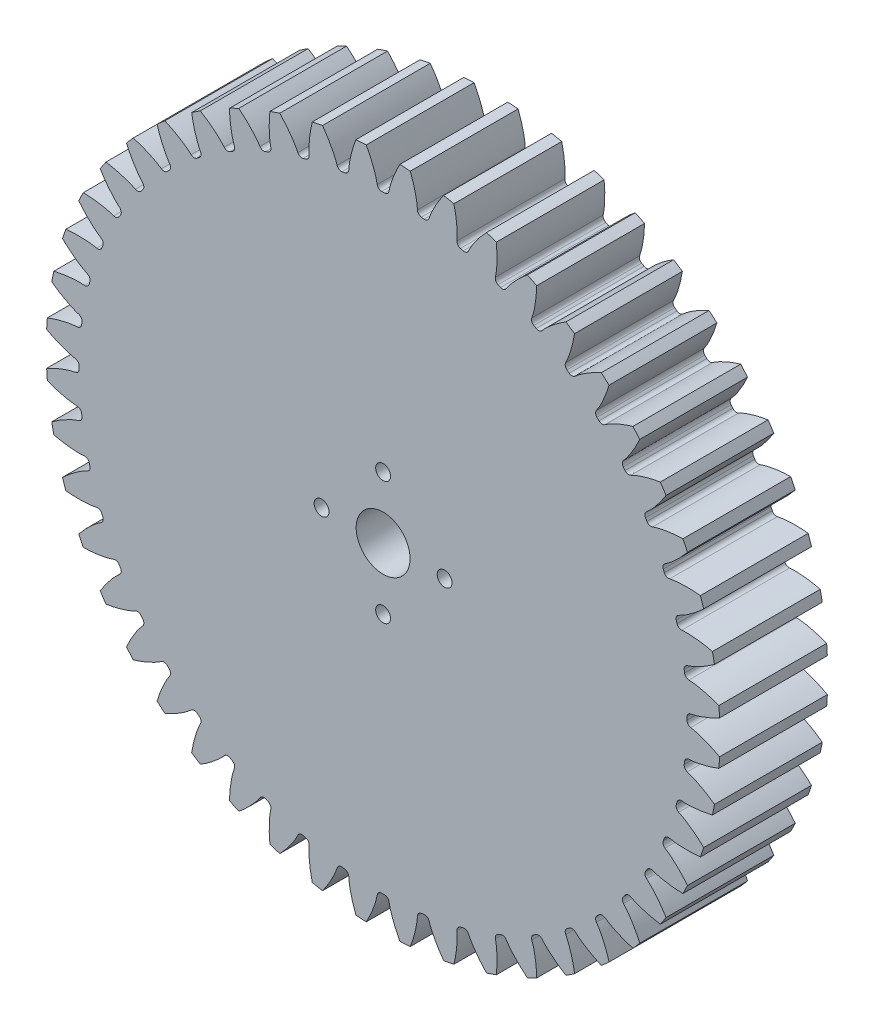
SolidWorks part; units mm, degrees
ref_plane "Front Plane" through (0, 0, 0) normal (0, 0, 1) x (1, 0, 0)
ref_plane "Top Plane" through (0, 0, 0) normal (0, 1, 0) x (1, 0, 0)
ref_plane "Right Plane" through (0, 0, 0) normal (1, 0, 0) x (0, 0, -1)
sketch "Sketch1" plane through (0, 0, 0) normal (0, 0, 1) x (1, 0, 0)
  line L0 (0, 0) -> (0, 38.1) construction
  line L1 (-12.2451, 42.5569) -> (12.2451, 33.6431) construction
  circle A0 centre (0, 0) radius 36.1156 construction
  circle A1 centre (0, 0) radius 39.6875 construction
  circle A2 centre (0, 0) radius 38.1 construction
  circle A3 centre (0, 0) radius 35.8023 construction
  circle A4 centre (0, 0) radius 3.175 construction
  circle A5 centre (0, 0) radius 6.35 construction
  point P8 (203.2, 0)
  point P13 (609.6, 0)
  dimension "OD | Outside Diameter" = 79.375
  dimension "Root Diameter" = 72.2313
  dimension "Gear Pitch Diameter" = 76.2
  dimension "Base Diameter" = 71.6046
  dimension "For Shaft Diameter" = 6.35
  dimension "Hub Diameter" = 12.7
  dimension "Pressure Angle" = 20
  dimension "Number of Teeth" = 1219.2
  dimension "Gear Pitch | Diametral Pitch" = 406.4
sketch "Sketch2" plane through (0, 0, 0) normal (1, 0, 0) x (0, 0, -1)
  line L0 (-6.35, 0) -> (6.35, 0) construction
  line L1 (-6.35, 39.6875) -> (6.35, 39.6875) construction
  point P2 (0, 39.6875)
  point P4 (-5.715, 0)
  point P6 (-5.715, 39.6875)
  dimension "Overall Width" = 12.7
  dimension "Face Width" = 12.065
sketch "Sketch3" plane through (0, 0, 0) normal (0, 0, 1) x (1, 0, 0)
  circle A0 centre (0, 0) radius 39.6875
  circle A1 centre (0, 0) radius 39.6875 construction
extrude "Boss-Extrude1" add sketch "Sketch3" against normal up to vertex (6.35 mm away) and the other way up to vertex (6.35 mm away) up to point (0, 0, -6.35) other way up to point (0, 0, 6.35)
sketch "Sketch4" plane through (0, 0, 0) normal (0, 0, 1) x (1, 0, 0)
  line L0 (0, 0) -> (35.7965, 0.638) construction
  line L2 (0, 0) -> (35.7965, -0.638) construction
  line L4 (35.7965, 0.638) -> (35.7966, 0.638)
  line L5 (35.7966, -0.638) -> (35.7965, -0.638)
  arc A0 (35.7965, 0.638) -> (35.7965, -0.638) centre (0, 0) cw
  arc A3 (39.6379, 1.9832) -> (39.6379, -1.9832) centre (0, 0) cw
  circle A4 centre (0, 0) radius 39.6875 construction
  spline S0 degree 4 poles (35.7966, 0.638) (35.8027, 0.6382) (35.8196, 0.6388) (35.8517, 0.6408) (35.904, 0.6452) (35.9707, 0.6523) (36.0567, 0.6632) (36.1581, 0.6785) (36.2693, 0.6976) (36.3903, 0.7211) (36.5108, 0.7468) (36.631, 0.7746) (36.7506, 0.8043) (36.8954, 0.8425) (37.0688, 0.8916) (37.2712, 0.9536) (37.5005, 1.0294) (37.7337, 1.1125) (37.9629, 1.1992) (38.1941, 1.2923) (38.4174, 1.3864) (38.649, 1.4898) (38.8625, 1.5882) (39.1012, 1.7047) (39.2937, 1.8006) (39.5471, 1.9338) (39.6965, 2.0146) (39.8712, 2.1113) (39.9487, 2.1555) (39.9964, 2.1827) knots 0 0 0 0 0 0.005377 0.015084 0.028532 0.04661 0.064855 0.092111 0.119476 0.146842 0.174209 0.201575 0.228941 0.256307 0.307035 0.361767 0.4165 0.471232 0.525964 0.580697 0.635429 0.690161 0.744894 0.799626 0.854358 0.909091 0.954545 1 1 1 1 1 construction
  spline S1 degree 4 poles (35.7966, 0.638) (35.8027, 0.6382) (35.8196, 0.6388) (35.8517, 0.6408) (35.904, 0.6452) (35.9707, 0.6523) (36.0567, 0.6632) (36.1581, 0.6785) (36.2693, 0.6976) (36.3903, 0.7211) (36.5108, 0.7468) (36.631, 0.7746) (36.7506, 0.8043) (36.8954, 0.8425) (37.0688, 0.8916) (37.2712, 0.9536) (37.5005, 1.0294) (37.7337, 1.1125) (37.9629, 1.1992) (38.1941, 1.2923) (38.4174, 1.3864) (38.649, 1.4898) (38.8625, 1.5882) (39.1012, 1.7047) (39.2937, 1.8006) (39.4921, 1.905) (39.5886, 1.9565) (39.6379, 1.9832) knots 0 0 0 0 0 0.005377 0.015084 0.028532 0.04661 0.064855 0.092111 0.119476 0.146842 0.174209 0.201575 0.228941 0.256307 0.307035 0.361767 0.4165 0.471232 0.525964 0.580697 0.635429 0.690161 0.744894 0.799626 0.854358 0.909091 0.909091 0.909091 0.909091 0.909091
  spline S2 degree 4 poles (35.7966, -0.638) (35.8027, -0.6382) (35.8196, -0.6388) (35.8517, -0.6408) (35.904, -0.6452) (35.9707, -0.6523) (36.0567, -0.6632) (36.1581, -0.6785) (36.2693, -0.6976) (36.3903, -0.7211) (36.5108, -0.7468) (36.631, -0.7746) (36.7506, -0.8043) (36.8954, -0.8425) (37.0688, -0.8916) (37.2712, -0.9536) (37.5005, -1.0294) (37.7337, -1.1125) (37.9629, -1.1992) (38.1941, -1.2923) (38.4174, -1.3864) (38.649, -1.4898) (38.8625, -1.5882) (39.1012, -1.7047) (39.2937, -1.8006) (39.5471, -1.9338) (39.6965, -2.0146) (39.8712, -2.1113) (39.9487, -2.1555) (39.9964, -2.1827) knots 0 0 0 0 0 0.005377 0.015084 0.028532 0.04661 0.064855 0.092111 0.119476 0.146842 0.174209 0.201575 0.228941 0.256307 0.307035 0.361767 0.4165 0.471232 0.525964 0.580697 0.635429 0.690161 0.744894 0.799626 0.854358 0.909091 0.954545 1 1 1 1 1 construction
  spline S3 degree 4 poles (35.7966, -0.638) (35.8027, -0.6382) (35.8196, -0.6388) (35.8517, -0.6408) (35.904, -0.6452) (35.9707, -0.6523) (36.0567, -0.6632) (36.1581, -0.6785) (36.2693, -0.6976) (36.3903, -0.7211) (36.5108, -0.7468) (36.631, -0.7746) (36.7506, -0.8043) (36.8954, -0.8425) (37.0688, -0.8916) (37.2712, -0.9536) (37.5005, -1.0294) (37.7337, -1.1125) (37.9629, -1.1992) (38.1941, -1.2923) (38.4174, -1.3864) (38.649, -1.4898) (38.8625, -1.5882) (39.1012, -1.7047) (39.2937, -1.8006) (39.4921, -1.905) (39.5886, -1.9565) (39.6379, -1.9832) knots 0 0 0 0 0 0.005377 0.015084 0.028532 0.04661 0.064855 0.092111 0.119476 0.146842 0.174209 0.201575 0.228941 0.256307 0.307035 0.361767 0.4165 0.471232 0.525964 0.580697 0.635429 0.690161 0.744894 0.799626 0.854358 0.909091 0.909091 0.909091 0.909091 0.909091
  dimension "D1" = 71.6043
extrude "Cut-Extrude1" cut sketch "Sketch4" against normal through all both and the other way through all
fillet "Fillet1" radius 0.5326 2 edges at (35.7965, -0.638, 0) (35.7965, 0.638, 0)
pattern_circular "CirPattern1" count 48 over 360 about axis through (0, 0, 6.35) along (0, 0, -1) of "Cut-Extrude1", "Fillet1"
sketch "Sketch6" plane through (0, 0, 0) normal (0, 1, 0) x (1, 0, 0)
  line L0 (0, 10.0524) -> (0, -11.762) construction
sketch "Sketch7" plane through (0, 0, 0) normal (0, 0, 1) x (1, 0, 0)
  circle A0 centre (7.25, 0) radius 0.877
  dimension "D2" = 1.754
  dimension "D1" = 7.25
extrude "Cut-Extrude2" cut sketch "Sketch7" against normal through all both and the other way through all
pattern_circular "CirPattern2" count 4 over 360 about axis through (0, 0, 0) along (0, 0, 1) of "Cut-Extrude2"
sketch "Sketch8" plane through (0, 0, 6.35) normal (0, 0, 1) x (1, 0, 0)
  circle A0 centre (0, 0) radius 3.175
  dimension "D1" = 6.35
extrude "Cut-Extrude3" cut sketch "Sketch8" against normal through all
equation "\"Root Diameter@Sketch1\"=\"Root Diameter\""
equation "\"OD | Outside Diameter@Sketch1\"=\"Outside Diameter\""
equation "\"D1@CirPattern1\"=\"Number of Teeth\""
equation "\"Diametral Pitch\"= 16"
equation "\"Number of Teeth\"= 48"
equation "\"Pressure Angle\"=20"
equation "\"Pitch Diameter\"= \"Number of Teeth\" / \"Diametral Pitch\""
equation "\"Base Diameter\"= \"Pitch Diameter\" * cos ( \"Pressure Angle\" )"
equation "\"Outside Diameter\"= ( \"Number of Teeth\" + 2 ) / \"Diametral Pitch\""
equation "\"Dedendum\"= 1.25 / \"Diametral Pitch\""
equation "\"Root Diameter\"= \"Pitch Diameter\" - ( 2 * \"Dedendum\" )"
equation "\"Pitch Angle\"= 360deg / \"Number of Teeth\""
equation "\"Alpha\"= sqr ( \"Pitch Diameter\" ^ 2 - \"Base Diameter\" ^ 2 ) / \"Base Diameter\" * 180 / PI - \"Pressure Angle\""
equation "\"Beta\"= ( \"Pitch Angle\" / 4 - \"Alpha\" )"
equation "\"Phi\"= sqr ( ( \"Outside Diameter\" / 2 ) ^ 2 - ( \"Base Diameter\" / 2 ) ^ 2 ) / ( \"Base Diameter\" / 2 )"
equation "\"Addendum\"= 1 / \"Diametral Pitch\""
equation "\"WorkingDepth\"= 2 / \"Diametral Pitch\""
equation "\"WholeDepth\"= 2.25 / \"Diametral Pitch\""
equation "\"Clearance\"= 0.25 / \"Diametral Pitch\""
equation "\"ToothThickness\"= ( pi * 2 ) / \"Diametral Pitch\""
equation "\"CircularPitch\"= pi / \"Diametral Pitch\""
equation "\"Number of Teeth@Sketch1\"=\"Number of Teeth\""
equation "\"Gear Pitch | Diametral Pitch@Sketch1\"=\"Diametral Pitch\""
equation "\"Pressure Angle@Sketch1\"=\"Pressure Angle\""
equation "\"Gear Pitch Diameter@Sketch1\"=\"Pitch Diameter\""
equation "\"Base Diameter@Sketch1\"=\"Base Diameter\""
equation "\"Fillet\"= \"Clearance\" * cos ( \"Pressure Angle\" ) * tan ( ( 90 + \"Pressure Angle\" ) / 2 )"
equation "\"D1@Fillet1\"=\"Fillet\""
equation "\"D1@Sketch4\"=if( \"Base Diameter\">\"Root Diameter\",\"Root Diameter\",\"Base Diameter\"-.00001)"
equation "\"D1@Fillet2\"=\"Fillet\""
equation "\"D1@Sketch7\"=7.25mm"
equation "\"D2@Sketch7\" = 1.5mm + \"normTol\""
equation "\"tightTol\"= 0.005in"
equation "\"normTol\"= 0.01in"
equation "\"looseTol\"= 0.02in"
